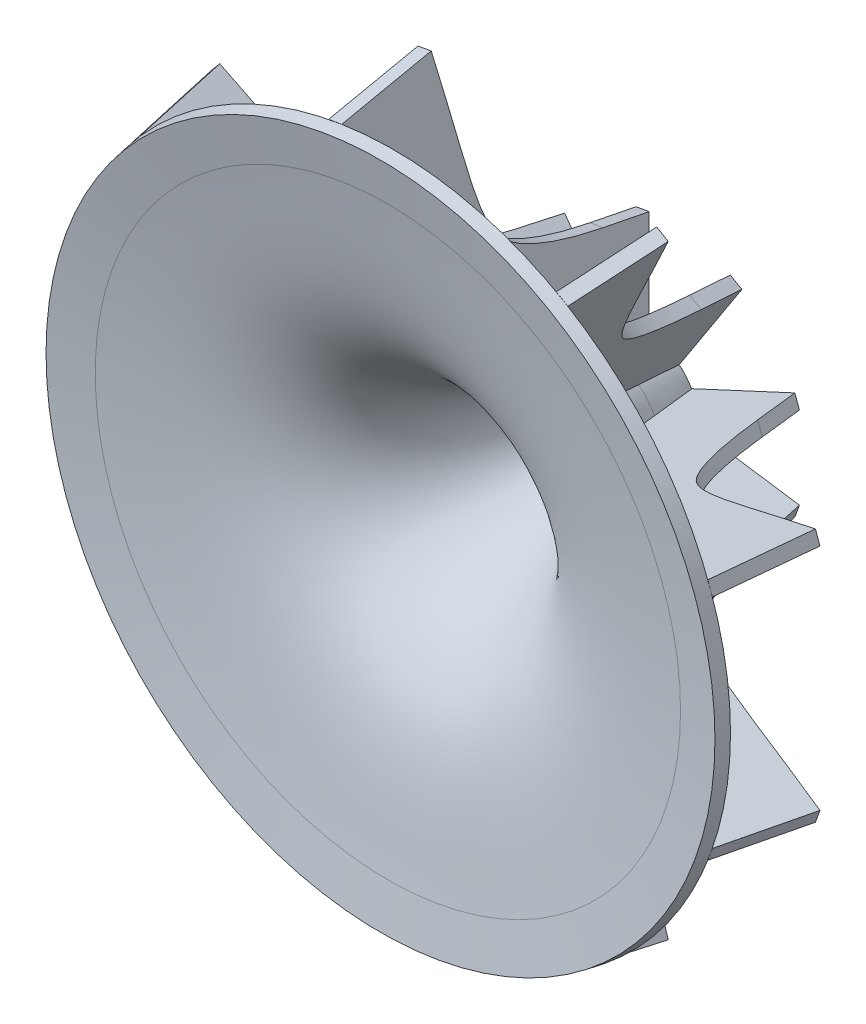
SolidWorks part; units mm, degrees
ref_plane "Front Plane" through (0, 0, 0) normal (0, 0, 1) x (1, 0, 0)
ref_plane "Top Plane" through (0, 0, 0) normal (0, 1, 0) x (1, 0, 0)
ref_plane "Right Plane" through (0, 0, 0) normal (1, 0, 0) x (0, 0, -1)
sketch "Sketch_of_Hub" plane through (0, 0, 0) normal (0, 1, 0) x (1, 0, 0)
  line L0 (-25, 0) -> (-21.875, 0.551)
  line L1 (-25, 0) -> (-2.5, 0) construction
  line L2 (-3.0878, 16.6667) -> (-2.5, 20)
  line L3 (-2.5, 0) -> (-2.5, 20) construction
  line L4 (-25.1736, 0.9848) -> (-22.0486, 1.5358)
  line L5 (-4.0726, 16.8403) -> (-3.4848, 20.1736)
  line L6 (-3.4848, 20.1736) -> (-2.5, 20)
  line L7 (-25.1736, 0.9848) -> (-25, 0)
  line L8 (0, -11.4107) -> (0, -1.4179) construction
  spline S0 degree 1 poles (-22.0486, 1.5358) (-4.0726, 16.8403) knots 0 0 1 1 construction
  spline S1 degree 3 poles (-21.875, 0.551) (-12.6553, 2.1767) (-5.6751, 1.9929) (-3.0878, 16.6667) knots 0 0 0 0 1 1 1 1
  spline S2 degree 3 poles (-22.0486, 1.5358) (-21.4781, 1.6364) (-20.318, 1.8298) (-18.1331, 2.1821) (-15.5731, 2.6349) (-12.8414, 3.3758) (-10.4654, 4.4784) (-8.4179, 6.109) (-6.9387, 8.1051) (-5.898, 10.2171) (-5.1966, 12.0843) (-4.6823, 13.9057) (-4.3193, 15.5169) (-4.1493, 16.4049) (-4.0726, 16.8403) knots 0 0 0 0 0.0625 0.125 0.25 0.375 0.5 0.625 0.75 0.8125 0.875 0.9375 0.96875 1 1 1 1
  point P8 (-12.5, 3.3259)
  point P9 (-12.5, 2.895)
  point P10 (-4.9614, 4.7386)
  point P11 (-6.7378, 5.6571)
  point P12 (-3.1355, 16.3956)
  point P18 (-5.9419, 7.3085)
  point P19 (0, 0)
  point P20 (-19.5122, 1.9525)
  point P21 (-6.9543, 7.2761)
  point P22 (-6.0285, 7.7655)
  point P23 (0, 0)
  point P24 (-7.3665, 6.3604)
  point P25 (0, 0)
  dimension "D1" = 2.5
  dimension "D2" = 20
  dimension "D3" = 25
  dimension "D4" = 10
  dimension "D5" = 10
  dimension "D7" = 3.3333
  dimension "D8" = 3.125
  dimension "D6" = 1
revolve "Hub" add sketch "Sketch_of_Hub" angle 360 about L8
sketch "Sketch9" plane through (0, 0, 0) normal (0, 1, 0) x (1, 0, 0)
  line L0 (-10.3785, 21.3892) -> (-10.9662, 18.0559)
  line L1 (-23.2642, 8.4295) -> (-26.3892, 7.8785)
  line L2 (-3.4848, 20.1736) -> (-10.3785, 21.3892)
  line L3 (-26.3892, 7.8785) -> (-25.1736, 0.9848)
  line L6 (-3.4848, 20.1736) -> (-4.0726, 16.8403)
  line L7 (-2.5, 20) -> (-3.4848, 20.1736)
  line L8 (-3.0878, 16.6667) -> (-2.5, 20)
  line L9 (-25, 0) -> (-21.875, 0.551)
  line L10 (-25.1736, 0.9848) -> (-25, 0)
  line L11 (-22.0486, 1.5358) -> (-25.1736, 0.9848)
  line L18 (-3.4848, 20.1736) -> (-4.0726, 16.8403)
  line L23 (-22.0486, 1.5358) -> (-25.1736, 0.9848)
  spline S0 degree 1 poles (-10.9662, 18.0559) (-23.2642, 8.4295) knots 0 0 1 1 construction
  spline S1 degree 3 poles (-10.9662, 18.0559) (-11.0308, 17.6896) (-11.1758, 16.9329) (-11.4686, 15.6357) (-11.8669, 14.2333) (-12.3467, 12.9687) (-12.9591, 11.7427) (-13.5694, 10.9776) (-14.1233, 10.5317) (-15.1348, 10.0236) (-16.689, 9.584) (-18.3596, 9.2514) (-19.8108, 9.002) (-21.4281, 8.7414) (-22.6662, 8.5349) (-23.2642, 8.4295) knots 0 0 0 0 0.03125 0.0625 0.125 0.1875 0.25 0.375 0.5 0.625 0.75 0.8125 0.875 0.9375 1 1 1 1
  spline S2 degree 3 poles (-106.1325, -995.8881) (-142.0874, 977.9655) (179.6787, -978.0787) (-157.3539, 1004.6818) knots -3.780329 -3.780329 -3.780329 -3.780329 4.006276 4.006276 4.006276 4.006276 only from (-21.875, 0.551) to (-3.0878, 16.6667)
  spline S3 degree 3 poles (-776.0265, -3907.7228) (-2.9928, 116.0692) (0.3333, 36.1691) (-4.6823, 13.9057) (-5.1966, 12.0843) (-5.898, 10.2171) (-6.9387, 8.1051) (-8.4179, 6.109) (-10.4654, 4.4784) (-12.8414, 3.3758) (-15.5731, 2.6349) (-18.1331, 2.1821) (-49.4462, -2.8661) (-131.4903, -20.9757) (3977.7068, 16.8999) knots -1.60226 -1.60226 -1.60226 -1.60226 0.03125 0.0625 0.125 0.1875 0.25 0.375 0.5 0.625 0.75 0.875 0.9375 4.333013 4.333013 4.333013 4.333013 only from (-4.0726, 16.8403) to (-22.0486, 1.5358)
  spline S5 degree 3 poles (-4.0726, 16.8403) (-4.1493, 16.4049) (-4.3193, 15.5169) (-4.6823, 13.9057) (-5.1966, 12.0843) (-5.898, 10.2171) (-6.9387, 8.1051) (-8.4179, 6.109) (-10.4654, 4.4784) (-12.8414, 3.3758) (-15.5731, 2.6349) (-18.1331, 2.1821) (-20.318, 1.8298) (-21.4781, 1.6364) (-22.0486, 1.5358) knots 0 0 0 0 0.03125 0.0625 0.125 0.1875 0.25 0.375 0.5 0.625 0.75 0.875 0.9375 1 1 1 1
  dimension "D1" = 0
  dimension "D2" = 7
extrude "Blade" add sketch "Sketch9" along normal mid plane 1 separate body
pattern_circular "CirPattern5" count 9 over 360 about axis through (0, 0, -20.1736) along (0, 0, 1) of bodies 102
equation "\"Hub_Vertical_Angle\" = 10"
equation "\"Hub_Horizontal_Angle\"=10"
equation "\"Hub_Hole_Radius\"= 2.5"
equation "\"Hub_Radius\"= 25"
equation "\"Hub_Height\"= 20"
equation "\"D2@Sketch_of_Hub\" = \"Hub_Height\""
equation "\"D3@Sketch_of_Hub\" = \"Hub_Radius\""
equation "\"D1@Sketch_of_Hub\" = \"Hub_Hole_Radius\""
equation "\"D4@Sketch_of_Hub\" = \"Hub_Horizontal_Angle\""
equation "\"D5@Sketch_of_Hub\" = \"Hub_Vertical_Angle\""
equation "\"Mouth_Vertical_Height\" = \"Hub_Height\" * 1 / 6"
equation "\"D7@Sketch_of_Hub\"=\"Mouth_Vertical_Height\""
equation "\"Exit_Horizontal_Length\"= \"Hub_Radius\" * 1 / 8"
equation "\"D8@Sketch_of_Hub\"=\"Exit_Horizontal_Length\""
